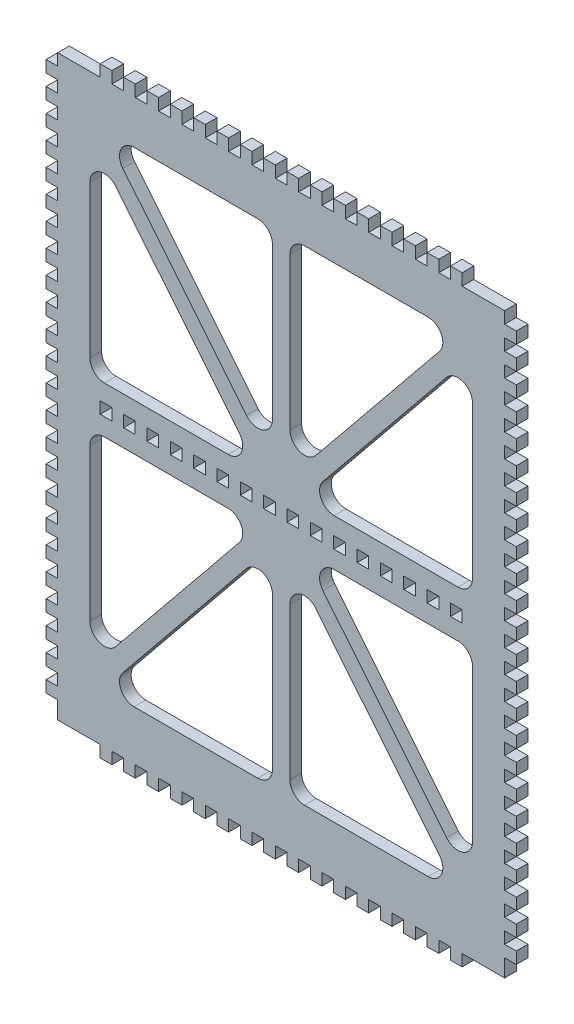
SolidWorks part; units mm, degrees
material "Cedar"
ref_plane "Front Plane" through (0, 0, 0) normal (0, 0, 1) x (1, 0, 0)
ref_plane "Top Plane" through (0, 0, 0) normal (0, 1, 0) x (1, 0, 0)
ref_plane "Right Plane" through (0, 0, 0) normal (1, 0, 0) x (0, 0, -1)
sketch "Sketch1" plane through (0, 0, 0) normal (0, 0, 1) x (1, 0, 0)
  line L0 (0, 0) -> (0, 50) construction
  line L1 (0, 0) -> (-64, 0) construction
  line L2 (-80.56, -100) -> (-80.56, 98)
  line L3 (-80.56, 98) -> (80.56, 98)
  line L5 (-50.3949, 83) -> (-8, 83)
  line L6 (5.3277, -9.8926) -> (7.6553, -8) construction
  line L7 (80.56, -100) -> (80.56, 98)
  line L8 (-80.56, -100) -> (80.56, -100)
  line L9 (3, -11.7852) -> (5.3277, -9.8926) construction
  line L10 (-56.6806, 68.2943) -> (-14.2856, 16.1544)
  line L11 (-18.1651, 8) -> (-60.56, 8)
  line L12 (8, 83) -> (50.3949, 83)
  line L13 (-54.2744, 74.8456) -> (-11.8794, 22.7057)
  line L14 (-3, 25.8601) -> (-3, 78)
  line L15 (57.9864, 69.9002) -> (53.3311, 73.6855) construction
  line L16 (3, 78) -> (3, 25.8601)
  line L17 (11.8794, 22.7057) -> (54.2744, 74.8456)
  line L18 (55.6587, 71.7929) -> (78.1199, 99.417) construction
  line L19 (56.6806, 68.2943) -> (14.2856, 16.1544)
  line L20 (18.1651, 8) -> (60.56, 8)
  line L21 (60.9047, 83) -> (63.2323, 81.1074) construction
  line L22 (63.2323, 81.1074) -> (65.56, 79.2148) construction
  line L23 (-67.1135, 90.6359) -> (-71.7688, 86.8507) construction
  line L24 (-71.7688, 86.8507) -> (-69.4411, 88.7433) construction
  line L25 (-69.4411, 88.7433) -> (-78.1554, 99.4607) construction
  line L26 (-60.9047, 83) -> (-63.2323, 81.1074) construction
  line L27 (-63.2323, 81.1074) -> (-65.56, 79.2148) construction
  line L28 (8.9351, -14.3292) -> (0.0045, -3.3459) construction
  line L29 (6.6074, -16.2219) -> (11.2627, -12.4366) construction
  line L30 (-5.3277, -9.8926) -> (-7.6553, -8) construction
  line L31 (-3, -11.7852) -> (-5.3277, -9.8926) construction
  line L32 (-9.7926, -15.3839) -> (0.7217, -2.4528) construction
  line L33 (-12.1203, -13.4913) -> (-9.7926, -15.3839) construction
  line L34 (-7.465, -17.2765) -> (-12.1203, -13.4913) construction
  line L35 (-63.2323, -81.1074) -> (-65.56, -79.2148) construction
  line L36 (-60.9047, -83) -> (-63.2323, -81.1074) construction
  line L37 (-71.7688, -86.8507) -> (-69.4411, -88.7433) construction
  line L38 (-67.1135, -90.6359) -> (-71.7688, -86.8507) construction
  line L39 (63.2323, -81.1074) -> (65.56, -79.2148) construction
  line L40 (60.9047, -83) -> (63.2323, -81.1074) construction
  line L41 (57.9864, -69.9002) -> (53.3311, -73.6855) construction
  line L42 (-65.56, -13) -> (-65.56, -65.1399)
  line L43 (65.56, -13) -> (65.56, -65.1399)
  line L44 (18.1651, -8) -> (60.56, -8)
  line L45 (56.6806, -68.2943) -> (14.2856, -16.1544)
  line L46 (65.56, 13) -> (65.56, 65.1399)
  line L47 (-65.56, 13) -> (-65.56, 65.1399)
  line L48 (-7.465, 17.2765) -> (-12.1203, 13.4913) construction
  line L49 (-12.1203, 13.4913) -> (-9.7926, 15.3839) construction
  line L50 (-9.7926, 15.3839) -> (0.7217, 2.4528) construction
  line L51 (-3, 11.7852) -> (-5.3277, 9.8926) construction
  line L52 (-5.3277, 9.8926) -> (-7.6553, 8) construction
  line L53 (6.6074, 16.2219) -> (11.2627, 12.4366) construction
  line L54 (8.9351, 14.3292) -> (0.0045, 3.3459) construction
  line L55 (3, 11.7852) -> (5.3277, 9.8926) construction
  line L56 (5.3277, 9.8926) -> (7.6553, 8) construction
  line L57 (11.8794, -22.7057) -> (54.2744, -74.8456)
  line L58 (3, -78) -> (3, -25.8601)
  line L59 (-3, -25.8601) -> (-3, -78)
  line L60 (-54.2744, -74.8456) -> (-11.8794, -22.7057)
  line L61 (8, -83) -> (50.3949, -83)
  line L62 (-18.1651, -8) -> (-60.56, -8)
  line L63 (-56.6806, -68.2943) -> (-14.2856, -16.1544)
  line L64 (-50.3949, -83) -> (-8, -83)
  arc A0 (56.6806, 68.2943) -> (65.56, 65.1399) centre (60.56, 65.1399) cw
  arc A1 (60.56, 8) -> (65.56, 13) centre (60.56, 13) ccw
  arc A2 (14.2856, 16.1544) -> (18.1651, 8) centre (18.1651, 13) ccw
  arc A3 (3, 25.8601) -> (11.8794, 22.7057) centre (8, 25.8601) ccw
  arc A4 (54.2744, 74.8456) -> (50.3949, 83) centre (50.3949, 78) ccw
  arc A5 (3, 78) -> (8, 83) centre (8, 78) cw
  arc A6 (-54.2744, 74.8456) -> (-50.3949, 83) centre (-50.3949, 78) cw
  arc A7 (-11.8794, 22.7057) -> (-3, 25.8601) centre (-8, 25.8601) ccw
  arc A8 (-3, 78) -> (-8, 83) centre (-8, 78) ccw
  arc A9 (-14.2856, 16.1544) -> (-18.1651, 8) centre (-18.1651, 13) cw
  arc A10 (-65.56, 13) -> (-60.56, 8) centre (-60.56, 13) ccw
  arc A11 (-56.6806, 68.2943) -> (-65.56, 65.1399) centre (-60.56, 65.1399) ccw
  arc A12 (-56.6806, -68.2943) -> (-65.56, -65.1399) centre (-60.56, -65.1399) cw
  arc A13 (-65.56, -13) -> (-60.56, -8) centre (-60.56, -13) cw
  arc A14 (-14.2856, -16.1544) -> (-18.1651, -8) centre (-18.1651, -13) ccw
  arc A15 (-3, -78) -> (-8, -83) centre (-8, -78) cw
  arc A16 (-11.8794, -22.7057) -> (-3, -25.8601) centre (-8, -25.8601) cw
  arc A17 (-54.2744, -74.8456) -> (-50.3949, -83) centre (-50.3949, -78) ccw
  arc A18 (3, -78) -> (8, -83) centre (8, -78) ccw
  arc A19 (54.2744, -74.8456) -> (50.3949, -83) centre (50.3949, -78) cw
  arc A20 (3, -25.8601) -> (11.8794, -22.7057) centre (8, -25.8601) cw
  arc A21 (14.2856, -16.1544) -> (18.1651, -8) centre (18.1651, -13) cw
  arc A22 (60.56, -8) -> (65.56, -13) centre (60.56, -13) cw
  arc A23 (56.6806, -68.2943) -> (65.56, -65.1399) centre (60.56, -65.1399) ccw
  point P19 (0, 83)
  point P21 (0, 98)
  point P27 (-64, 0)
  point P28 (64, 0)
  point P29 (87, 0)
  point P34 (-87, 0)
  point P76 (65.56, 8)
  point P88 (3, 83)
  point P97 (-3, 83)
  point P103 (-65.56, 8)
  point P144 (-65.56, -8)
  point P145 (-3, -83)
  point P146 (3, -83)
  point P147 (65.56, -8)
  point P148 (0, -83)
  dimension "D3" = 15
  dimension "D8" = 98
  dimension "D7" = 6
  dimension "D9" = 6
  dimension "D10" = 8
  dimension "D11" = 100
  dimension "D12" = 5
  dimension "D2" = 161.12
  dimension "D4" = 15
  dimension "D5" = 3
  dimension "D6" = 3
  dimension "D13" = 15
extrude "Boss-Extrude1" add sketch "Sketch1" along normal blind 4
sketch "Sketch2" plane through (0, 0, 4) normal (0, 0, 1) x (1, 0, 0)
  line L0 (0, 0) -> (-89.2695, 0) construction
  line L1 (0, 0) -> (0, 71.1996) construction
  line L2 (-80.56, -50) -> (-76.56, -50)
  line L4 (-80.56, -100) -> (-80.56, 98) construction
  line L5 (-80.56, 86) -> (-76.56, 86)
  line L6 (-80.56, 86) -> (-80.56, 90)
  line L7 (-80.56, 90) -> (-76.56, 90)
  line L8 (-76.56, 86) -> (-76.56, 90)
  line L9 (-80.56, 78) -> (-76.56, 78)
  line L10 (-80.56, 78) -> (-80.56, 82)
  line L11 (-80.56, 82) -> (-76.56, 82)
  line L12 (-76.56, 78) -> (-76.56, 82)
  line L13 (-80.56, 70) -> (-76.56, 70)
  line L14 (-80.56, 70) -> (-80.56, 74)
  line L15 (-80.56, 74) -> (-76.56, 74)
  line L16 (-76.56, 70) -> (-76.56, 74)
  line L17 (-80.56, 62) -> (-76.56, 62)
  line L18 (-80.56, 62) -> (-80.56, 66)
  line L19 (-80.56, 66) -> (-76.56, 66)
  line L20 (-76.56, 62) -> (-76.56, 66)
  line L21 (-80.56, 54) -> (-76.56, 54)
  line L22 (-80.56, 54) -> (-80.56, 58)
  line L23 (-80.56, 58) -> (-76.56, 58)
  line L24 (-76.56, 54) -> (-76.56, 58)
  line L25 (-80.56, 46) -> (-76.56, 46)
  line L26 (-80.56, 46) -> (-80.56, 50)
  line L27 (-80.56, 50) -> (-76.56, 50)
  line L28 (-76.56, 46) -> (-76.56, 50)
  line L29 (-80.56, 38) -> (-76.56, 38)
  line L30 (-80.56, 38) -> (-80.56, 42)
  line L31 (-80.56, 42) -> (-76.56, 42)
  line L32 (-76.56, 38) -> (-76.56, 42)
  line L33 (-80.56, 30) -> (-76.56, 30)
  line L34 (-80.56, 30) -> (-80.56, 34)
  line L35 (-80.56, 34) -> (-76.56, 34)
  line L36 (-76.56, 30) -> (-76.56, 34)
  line L37 (-80.56, 22) -> (-76.56, 22)
  line L38 (-80.56, 22) -> (-80.56, 26)
  line L39 (-80.56, 26) -> (-76.56, 26)
  line L40 (-76.56, 22) -> (-76.56, 26)
  line L41 (-80.56, 14) -> (-76.56, 14)
  line L42 (-80.56, 14) -> (-80.56, 18)
  line L43 (-80.56, 18) -> (-76.56, 18)
  line L44 (-76.56, 14) -> (-76.56, 18)
  line L45 (-80.56, 6) -> (-76.56, 6)
  line L46 (-80.56, 6) -> (-80.56, 10)
  line L47 (-80.56, 10) -> (-76.56, 10)
  line L48 (-76.56, 6) -> (-76.56, 10)
  line L49 (-80.56, -2) -> (-76.56, -2)
  line L50 (-80.56, -2) -> (-80.56, 2)
  line L51 (-80.56, 2) -> (-76.56, 2)
  line L52 (-76.56, -2) -> (-76.56, 2)
  line L53 (-80.56, -10) -> (-76.56, -10)
  line L54 (-80.56, -10) -> (-80.56, -6)
  line L55 (-80.56, -6) -> (-76.56, -6)
  line L56 (-76.56, -10) -> (-76.56, -6)
  line L57 (-80.56, -18) -> (-76.56, -18)
  line L58 (-80.56, -18) -> (-80.56, -14)
  line L59 (-80.56, -14) -> (-76.56, -14)
  line L60 (-76.56, -18) -> (-76.56, -14)
  line L61 (-80.56, -26) -> (-76.56, -26)
  line L62 (-80.56, -26) -> (-80.56, -22)
  line L63 (-80.56, -22) -> (-76.56, -22)
  line L64 (-76.56, -26) -> (-76.56, -22)
  line L65 (-80.56, -34) -> (-76.56, -34)
  line L66 (-80.56, -34) -> (-80.56, -30)
  line L67 (-80.56, -30) -> (-76.56, -30)
  line L68 (-76.56, -34) -> (-76.56, -30)
  line L69 (-80.56, -42) -> (-76.56, -42)
  line L70 (-80.56, -42) -> (-80.56, -38)
  line L71 (-80.56, -38) -> (-76.56, -38)
  line L72 (-76.56, -42) -> (-76.56, -38)
  line L73 (76.56, -90) -> (76.56, -86)
  line L74 (80.56, -86) -> (76.56, -86)
  line L75 (80.56, -90) -> (80.56, -86)
  line L76 (80.56, -90) -> (76.56, -90)
  line L77 (76.56, -82) -> (76.56, -78)
  line L78 (80.56, -78) -> (76.56, -78)
  line L79 (80.56, -82) -> (80.56, -78)
  line L80 (80.56, -82) -> (76.56, -82)
  line L81 (76.56, -74) -> (76.56, -70)
  line L82 (80.56, -70) -> (76.56, -70)
  line L83 (80.56, -74) -> (80.56, -70)
  line L84 (80.56, -74) -> (76.56, -74)
  line L85 (76.56, -66) -> (76.56, -62)
  line L86 (80.56, -62) -> (76.56, -62)
  line L87 (80.56, -66) -> (80.56, -62)
  line L88 (80.56, -66) -> (76.56, -66)
  line L89 (76.56, -58) -> (76.56, -54)
  line L90 (80.56, -54) -> (76.56, -54)
  line L91 (80.56, -58) -> (80.56, -54)
  line L92 (80.56, -58) -> (76.56, -58)
  line L93 (76.56, -50) -> (76.56, -46)
  line L94 (80.56, -46) -> (76.56, -46)
  line L95 (80.56, -50) -> (80.56, -46)
  line L96 (76.56, 94) -> (76.56, 98)
  line L97 (80.56, 98) -> (76.56, 98)
  line L98 (80.56, 94) -> (80.56, 98)
  line L99 (80.56, 94) -> (76.56, 94)
  line L100 (76.56, -42) -> (76.56, -38)
  line L101 (80.56, -38) -> (76.56, -38)
  line L102 (80.56, -42) -> (80.56, -38)
  line L103 (-80.56, 94) -> (-76.56, 94)
  line L104 (-80.56, 94) -> (-80.56, 98)
  line L105 (-80.56, 98) -> (-76.56, 98)
  line L106 (-76.56, 94) -> (-76.56, 98)
  line L107 (80.56, -42) -> (76.56, -42)
  line L108 (76.56, -34) -> (76.56, -30)
  line L109 (80.56, -30) -> (76.56, -30)
  line L110 (80.56, -34) -> (80.56, -30)
  line L111 (80.56, -34) -> (76.56, -34)
  line L112 (76.56, -26) -> (76.56, -22)
  line L113 (80.56, -22) -> (76.56, -22)
  line L114 (80.56, -26) -> (80.56, -22)
  line L115 (80.56, -26) -> (76.56, -26)
  line L116 (76.56, -18) -> (76.56, -14)
  line L117 (80.56, -14) -> (76.56, -14)
  line L118 (80.56, -18) -> (80.56, -14)
  line L119 (80.56, -18) -> (76.56, -18)
  line L120 (76.56, -10) -> (76.56, -6)
  line L121 (80.56, -6) -> (76.56, -6)
  line L122 (80.56, -10) -> (80.56, -6)
  line L123 (80.56, -10) -> (76.56, -10)
  line L124 (76.56, -2) -> (76.56, 2)
  line L125 (80.56, 2) -> (76.56, 2)
  line L126 (80.56, -2) -> (80.56, 2)
  line L127 (80.56, -2) -> (76.56, -2)
  line L128 (76.56, 6) -> (76.56, 10)
  line L129 (80.56, 10) -> (76.56, 10)
  line L130 (80.56, 6) -> (80.56, 10)
  line L131 (-80.56, -50) -> (-80.56, -46)
  line L132 (80.56, 6) -> (76.56, 6)
  line L133 (76.56, 14) -> (76.56, 18)
  line L134 (80.56, 18) -> (76.56, 18)
  line L135 (80.56, 14) -> (80.56, 18)
  line L136 (80.56, 14) -> (76.56, 14)
  line L137 (76.56, 22) -> (76.56, 26)
  line L138 (80.56, 26) -> (76.56, 26)
  line L139 (80.56, 22) -> (80.56, 26)
  line L140 (80.56, 22) -> (76.56, 22)
  line L141 (76.56, 30) -> (76.56, 34)
  line L142 (80.56, 34) -> (76.56, 34)
  line L143 (80.56, 30) -> (80.56, 34)
  line L144 (80.56, 30) -> (76.56, 30)
  line L145 (76.56, 38) -> (76.56, 42)
  line L146 (80.56, 42) -> (76.56, 42)
  line L147 (80.56, 38) -> (80.56, 42)
  line L148 (80.56, 38) -> (76.56, 38)
  line L149 (76.56, 46) -> (76.56, 50)
  line L150 (-80.56, -46) -> (-76.56, -46)
  line L151 (-76.56, -50) -> (-76.56, -46)
  line L152 (-80.56, -58) -> (-76.56, -58)
  line L153 (-80.56, -58) -> (-80.56, -54)
  line L154 (-80.56, -54) -> (-76.56, -54)
  line L155 (-76.56, -58) -> (-76.56, -54)
  line L156 (-80.56, -66) -> (-76.56, -66)
  line L157 (-80.56, -66) -> (-80.56, -62)
  line L158 (-80.56, -62) -> (-76.56, -62)
  line L159 (-76.56, -66) -> (-76.56, -62)
  line L160 (-80.56, -74) -> (-76.56, -74)
  line L161 (-80.56, -74) -> (-80.56, -70)
  line L162 (-80.56, -70) -> (-76.56, -70)
  line L163 (-76.56, -74) -> (-76.56, -70)
  line L164 (-80.56, -82) -> (-76.56, -82)
  line L165 (-80.56, -82) -> (-80.56, -78)
  line L166 (-80.56, -78) -> (-76.56, -78)
  line L167 (-76.56, -82) -> (-76.56, -78)
  line L168 (-80.56, -90) -> (-76.56, -90)
  line L169 (-80.56, -90) -> (-80.56, -86)
  line L170 (-80.56, -86) -> (-76.56, -86)
  line L171 (-76.56, -90) -> (-76.56, -86)
  line L172 (80.56, 50) -> (76.56, 50)
  line L173 (80.56, 46) -> (80.56, 50)
  line L174 (80.56, 46) -> (76.56, 46)
  line L175 (76.56, 54) -> (76.56, 58)
  line L176 (80.56, 58) -> (76.56, 58)
  line L177 (80.56, 54) -> (80.56, 58)
  line L178 (80.56, 54) -> (76.56, 54)
  line L179 (76.56, 62) -> (76.56, 66)
  line L180 (80.56, 66) -> (76.56, 66)
  line L181 (80.56, 62) -> (80.56, 66)
  line L182 (80.56, 62) -> (76.56, 62)
  line L183 (76.56, 70) -> (76.56, 74)
  line L184 (80.56, 74) -> (76.56, 74)
  line L185 (80.56, 70) -> (80.56, 74)
  line L186 (80.56, 70) -> (76.56, 70)
  line L187 (76.56, 78) -> (76.56, 82)
  line L188 (80.56, 82) -> (76.56, 82)
  line L189 (80.56, 78) -> (80.56, 82)
  line L190 (80.56, 78) -> (76.56, 78)
  line L191 (76.56, 86) -> (76.56, 90)
  line L192 (80.56, 90) -> (76.56, 90)
  line L193 (80.56, 86) -> (80.56, 90)
  line L194 (80.56, 86) -> (76.56, 86)
  line L195 (80.56, -50) -> (76.56, -50)
  line L196 (-80.56, 98) -> (80.56, 98) construction
  line L197 (-80.56, -100) -> (-76.56, -100)
  line L198 (-80.56, -100) -> (-80.56, -94)
  line L199 (-80.56, -94) -> (-76.56, -94)
  line L200 (-76.56, -100) -> (-76.56, -94)
  line L201 (80.56, -100) -> (76.56, -100)
  line L202 (80.56, -100) -> (80.56, -94)
  line L203 (80.56, -94) -> (76.56, -94)
  line L204 (76.56, -100) -> (76.56, -94)
  dimension "D1" = 4
  dimension "D2" = 4
  dimension "D3" = 4
  dimension "D4" = 24
  dimension "D5" = 4
extrude "Cut-Extrude1" cut sketch "Sketch2" against normal blind 4
sketch "Sketch3" plane through (0, 0, 4) normal (0, 0, 1) x (1, 0, 0)
  line L0 (0, 98) -> (0, 113.2766) construction
  line L1 (0, -1) -> (-32, -1) construction
  line L3 (-80.56, 98) -> (80.56, 98) construction
  line L4 (-2, 98) -> (-6, 98)
  line L5 (-2, 98) -> (-2, 102)
  line L6 (-2, 102) -> (-6, 102)
  line L7 (-6, 98) -> (-6, 102)
  line L8 (-10, 98) -> (-14, 98)
  line L9 (-10, 98) -> (-10, 102)
  line L10 (-10, 102) -> (-14, 102)
  line L11 (-14, 98) -> (-14, 102)
  line L12 (-18, 98) -> (-22, 98)
  line L13 (-18, 98) -> (-18, 102)
  line L14 (-18, 102) -> (-22, 102)
  line L15 (-22, 98) -> (-22, 102)
  line L16 (-26, 98) -> (-30, 98)
  line L17 (-26, 98) -> (-26, 102)
  line L18 (-26, 102) -> (-30, 102)
  line L19 (-30, 98) -> (-30, 102)
  line L20 (-34, 98) -> (-38, 98)
  line L21 (-34, 98) -> (-34, 102)
  line L22 (-34, 102) -> (-38, 102)
  line L23 (-38, 98) -> (-38, 102)
  line L24 (-42, 98) -> (-46, 98)
  line L25 (-42, 98) -> (-42, 102)
  line L26 (-42, 102) -> (-46, 102)
  line L27 (-46, 98) -> (-46, 102)
  line L28 (-50, 98) -> (-54, 98)
  line L29 (-50, 98) -> (-50, 102)
  line L30 (-50, 102) -> (-54, 102)
  line L31 (-54, 98) -> (-54, 102)
  line L32 (-58, 98) -> (-62, 98)
  line L33 (-58, 98) -> (-58, 102)
  line L34 (-58, 102) -> (-62, 102)
  line L35 (-62, 98) -> (-62, 102)
  line L36 (62, 98) -> (62, 102)
  line L37 (58, 102) -> (62, 102)
  line L38 (58, 98) -> (58, 102)
  line L39 (58, 98) -> (62, 98)
  line L40 (54, 98) -> (54, 102)
  line L41 (50, 102) -> (54, 102)
  line L42 (50, 98) -> (50, 102)
  line L43 (50, 98) -> (54, 98)
  line L44 (46, 98) -> (46, 102)
  line L45 (42, 102) -> (46, 102)
  line L46 (42, 98) -> (42, 102)
  line L47 (42, 98) -> (46, 98)
  line L48 (38, 98) -> (38, 102)
  line L49 (34, 102) -> (38, 102)
  line L50 (34, 98) -> (34, 102)
  line L51 (34, 98) -> (38, 98)
  line L52 (30, 98) -> (30, 102)
  line L53 (26, 102) -> (30, 102)
  line L54 (26, 98) -> (26, 102)
  line L55 (26, 98) -> (30, 98)
  line L56 (22, 98) -> (22, 102)
  line L57 (18, 102) -> (22, 102)
  line L58 (18, 98) -> (18, 102)
  line L59 (18, 98) -> (22, 98)
  line L60 (14, 98) -> (14, 102)
  line L61 (10, 102) -> (14, 102)
  line L62 (10, 98) -> (10, 102)
  line L63 (10, 98) -> (14, 98)
  line L64 (6, 98) -> (6, 102)
  line L65 (2, 102) -> (6, 102)
  line L66 (2, 98) -> (2, 102)
  line L67 (2, 98) -> (6, 98)
  line L68 (2, -100) -> (6, -100)
  line L69 (2, -100) -> (2, -104)
  line L70 (2, -104) -> (6, -104)
  line L71 (6, -100) -> (6, -104)
  line L72 (10, -100) -> (14, -100)
  line L73 (10, -100) -> (10, -104)
  line L74 (10, -104) -> (14, -104)
  line L75 (14, -100) -> (14, -104)
  line L76 (18, -100) -> (22, -100)
  line L77 (18, -100) -> (18, -104)
  line L78 (18, -104) -> (22, -104)
  line L79 (22, -100) -> (22, -104)
  line L80 (26, -100) -> (30, -100)
  line L81 (26, -100) -> (26, -104)
  line L82 (26, -104) -> (30, -104)
  line L83 (30, -100) -> (30, -104)
  line L84 (34, -100) -> (38, -100)
  line L85 (34, -100) -> (34, -104)
  line L86 (34, -104) -> (38, -104)
  line L87 (38, -100) -> (38, -104)
  line L88 (42, -100) -> (46, -100)
  line L89 (42, -100) -> (42, -104)
  line L90 (42, -104) -> (46, -104)
  line L91 (46, -100) -> (46, -104)
  line L92 (50, -100) -> (54, -100)
  line L93 (50, -100) -> (50, -104)
  line L94 (50, -104) -> (54, -104)
  line L95 (54, -100) -> (54, -104)
  line L96 (58, -100) -> (62, -100)
  line L97 (58, -100) -> (58, -104)
  line L98 (58, -104) -> (62, -104)
  line L99 (62, -100) -> (62, -104)
  line L100 (-62, -100) -> (-62, -104)
  line L101 (-58, -104) -> (-62, -104)
  line L102 (-58, -100) -> (-58, -104)
  line L103 (-58, -100) -> (-62, -100)
  line L104 (-54, -100) -> (-54, -104)
  line L105 (-50, -104) -> (-54, -104)
  line L106 (-50, -100) -> (-50, -104)
  line L107 (-50, -100) -> (-54, -100)
  line L108 (-46, -100) -> (-46, -104)
  line L109 (-42, -104) -> (-46, -104)
  line L110 (-42, -100) -> (-42, -104)
  line L111 (-42, -100) -> (-46, -100)
  line L112 (-38, -100) -> (-38, -104)
  line L113 (-34, -104) -> (-38, -104)
  line L114 (-34, -100) -> (-34, -104)
  line L115 (-34, -100) -> (-38, -100)
  line L116 (-30, -100) -> (-30, -104)
  line L117 (-26, -104) -> (-30, -104)
  line L118 (-26, -100) -> (-26, -104)
  line L119 (-26, -100) -> (-30, -100)
  line L120 (-22, -100) -> (-22, -104)
  line L121 (-18, -104) -> (-22, -104)
  line L122 (-18, -100) -> (-18, -104)
  line L123 (-18, -100) -> (-22, -100)
  line L124 (-14, -100) -> (-14, -104)
  line L125 (-10, -104) -> (-14, -104)
  line L126 (-10, -100) -> (-10, -104)
  line L127 (-10, -100) -> (-14, -100)
  line L128 (-6, -100) -> (-6, -104)
  line L129 (-2, -104) -> (-6, -104)
  line L130 (-2, -100) -> (-2, -104)
  line L131 (-2, -100) -> (-6, -100)
  line L132 (0, 98) -> (0, -100) construction
  line L133 (-80.56, -100) -> (80.56, -100) construction
  dimension "D1" = 2
  dimension "D2" = 4
  dimension "D3" = 4
  dimension "D4" = 8
extrude "Boss-Extrude2" add sketch "Sketch3" against normal blind 4
sketch "Sketch4" plane through (0, 0, 4) normal (0, 0, 1) x (1, 0, 0)
  line L0 (66.6117, 98) -> (66.6117, -100) construction
  line L1 (-80.56, 98) -> (80.56, 98) construction
  line L2 (-80.56, -100) -> (80.56, -100) construction
  line L3 (66.6117, -2) -> (19.488, -2) construction
  line L4 (0, 0) -> (0, 32.475) construction
  line L5 (0, 0) -> (0, 50) construction
  line L6 (14, -2) -> (14, 2)
  line L7 (2, -2) -> (6, -2)
  line L8 (2, -2) -> (2, 2)
  line L9 (2, 2) -> (6, 2)
  line L10 (6, -2) -> (6, 2)
  line L11 (10, 2) -> (14, 2)
  line L12 (10, -2) -> (10, 2)
  line L13 (10, -2) -> (14, -2)
  line L14 (22, -2) -> (22, 2)
  line L15 (18, 2) -> (22, 2)
  line L16 (18, -2) -> (18, 2)
  line L17 (18, -2) -> (22, -2)
  line L18 (30, -2) -> (30, 2)
  line L19 (26, 2) -> (30, 2)
  line L20 (26, -2) -> (26, 2)
  line L21 (26, -2) -> (30, -2)
  line L22 (38, -2) -> (38, 2)
  line L23 (34, 2) -> (38, 2)
  line L24 (34, -2) -> (34, 2)
  line L25 (34, -2) -> (38, -2)
  line L26 (46, -2) -> (46, 2)
  line L27 (42, 2) -> (46, 2)
  line L28 (42, -2) -> (42, 2)
  line L29 (42, -2) -> (46, -2)
  line L30 (54, -2) -> (54, 2)
  line L31 (50, 2) -> (54, 2)
  line L32 (50, -2) -> (50, 2)
  line L33 (50, -2) -> (54, -2)
  line L34 (62, -2) -> (62, 2)
  line L35 (58, 2) -> (62, 2)
  line L36 (58, -2) -> (58, 2)
  line L37 (58, -2) -> (62, -2)
  line L38 (-58, -2) -> (-62, -2)
  line L39 (-58, -2) -> (-58, 2)
  line L40 (-58, 2) -> (-62, 2)
  line L41 (-62, -2) -> (-62, 2)
  line L42 (-50, -2) -> (-54, -2)
  line L43 (-50, -2) -> (-50, 2)
  line L44 (-50, 2) -> (-54, 2)
  line L45 (-54, -2) -> (-54, 2)
  line L46 (-42, -2) -> (-46, -2)
  line L47 (-42, -2) -> (-42, 2)
  line L48 (-42, 2) -> (-46, 2)
  line L49 (-46, -2) -> (-46, 2)
  line L50 (-34, -2) -> (-38, -2)
  line L51 (-34, -2) -> (-34, 2)
  line L52 (-34, 2) -> (-38, 2)
  line L53 (-38, -2) -> (-38, 2)
  line L54 (-26, -2) -> (-30, -2)
  line L55 (-26, -2) -> (-26, 2)
  line L56 (-26, 2) -> (-30, 2)
  line L57 (-30, -2) -> (-30, 2)
  line L58 (-18, -2) -> (-22, -2)
  line L59 (-18, -2) -> (-18, 2)
  line L60 (-18, 2) -> (-22, 2)
  line L61 (-22, -2) -> (-22, 2)
  line L62 (-10, -2) -> (-14, -2)
  line L63 (-10, -2) -> (-10, 2)
  line L64 (-10, 2) -> (-14, 2)
  line L65 (-6, -2) -> (-6, 2)
  line L66 (-2, 2) -> (-6, 2)
  line L67 (-2, -2) -> (-2, 2)
  line L68 (-2, -2) -> (-6, -2)
  line L69 (-14, -2) -> (-14, 2)
  dimension "D1" = 100
  dimension "D2" = 4
  dimension "D3" = 4
  dimension "D4" = 2
  dimension "D5" = 8
extrude "Cut-Extrude2" cut sketch "Sketch4" against normal blind 10
